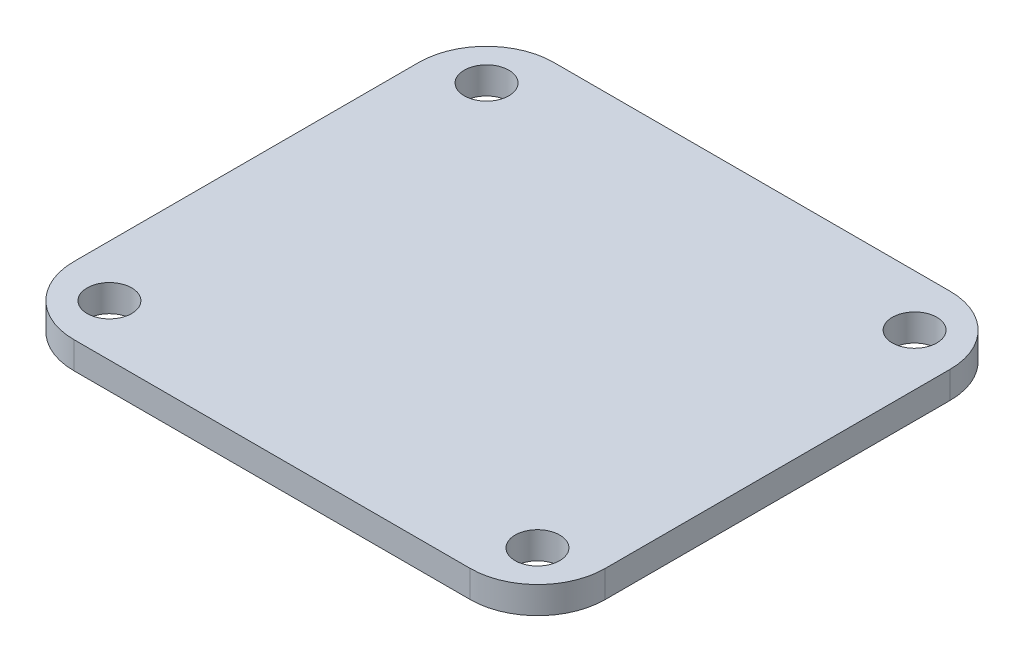
SolidWorks part; units mm, degrees
ref_plane "Plan de face" through (0, 0, 0) normal (0, 0, 1) x (1, 0, 0)
ref_plane "Plan de dessus" through (0, 0, 0) normal (0, 1, 0) x (1, 0, 0)
ref_plane "Plan de droite" through (0, 0, 0) normal (1, 0, 0) x (0, 0, -1)
sketch "Esquisse1" plane through (0, 0, 0) normal (0, 1, 0) x (1, 0, 0)
  line L1 (-19.685, 17.78) -> (19.685, 17.78)
  line L2 (-19.685, 17.78) -> (-19.685, -17.78)
  line L3 (-19.685, -17.78) -> (19.685, -17.78)
  line L4 (19.685, 17.78) -> (19.685, -17.78)
  line L5 (-19.685, 17.78) -> (19.685, -17.78) construction
  line L6 (-19.685, -17.78) -> (19.685, 17.78) construction
  line L7 (-15.855, 13.97) -> (15.855, 13.97) construction
  line L8 (-15.855, 13.97) -> (-15.855, -13.97) construction
  line L9 (-15.855, -13.97) -> (15.855, -13.97) construction
  line L10 (15.855, 13.97) -> (15.855, -13.97) construction
  line L11 (-15.855, 13.97) -> (15.855, -13.97) construction
  line L12 (-15.855, -13.97) -> (15.855, 13.97) construction
  circle A0 centre (-15.855, 13.97) radius 1.65
  circle A1 centre (15.855, 13.97) radius 1.65
  circle A2 centre (-15.855, -13.97) radius 1.65
  circle A3 centre (15.855, -13.97) radius 1.65
  point P0 (0, 0)
  point P6 (0, 0)
  dimension "D5" = 3.3
  dimension "D6" = 3.3
  dimension "D7" = 3.3
  dimension "D8" = 3.3
  dimension "D1" = 39.37
  dimension "D2" = 35.56
  dimension "D3" = 27.94
  dimension "D4" = 31.71
extrude "Boss.-Extru.1" add sketch "Esquisse1" along normal blind 2
fillet "Congé2" radius 5 4 edges at (-19.685, 1, -17.78) (-19.685, 1, 17.78) (19.685, 1, -17.78) (19.685, 1, 17.78)
